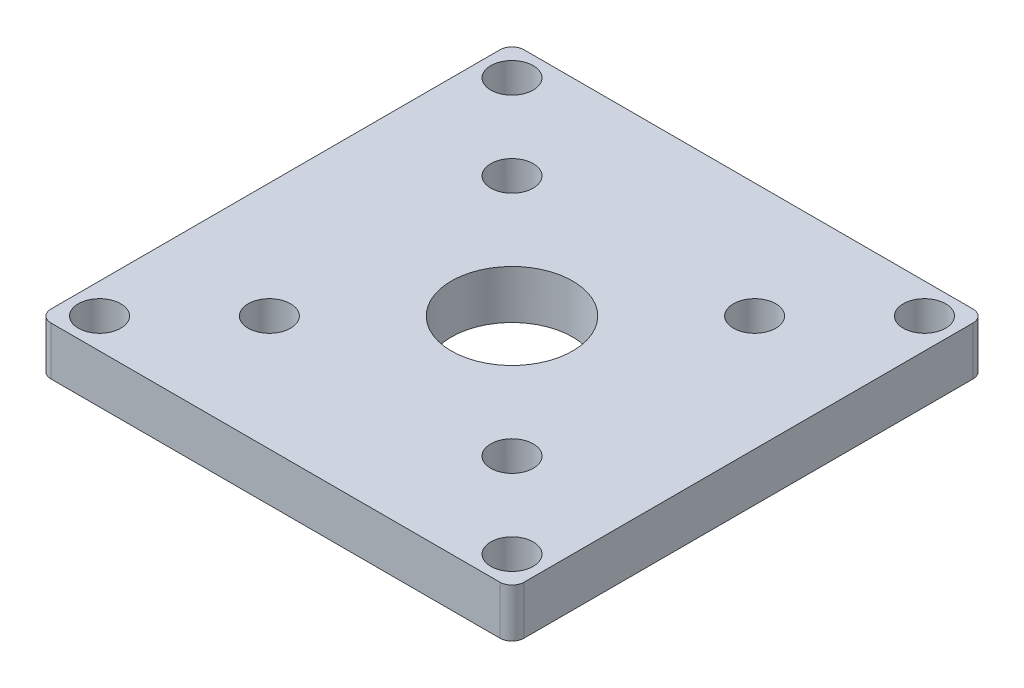
SolidWorks part; units mm, degrees
ref_plane "Front Plane" through (0, 0, 0) normal (0, 0, 1) x (1, 0, 0)
ref_plane "Top Plane" through (0, 0, 0) normal (0, 1, 0) x (1, 0, 0)
ref_plane "Right Plane" through (0, 0, 0) normal (1, 0, 0) x (0, 0, -1)
sketch "Sketch1" plane through (0, 0, 0) normal (0, 1, 0) x (1, 0, 0)
  line L5 (-17, -17) -> (17, -17) construction
  line L6 (-17, -17) -> (-17, 17) construction
  line L7 (-17, 17) -> (17, 17) construction
  line L8 (17, -17) -> (17, 17) construction
  line L9 (-17, -17) -> (17, 17) construction
  line L10 (-17, 17) -> (17, -17) construction
  line L11 (-19.5, -19.5) -> (19.5, -19.5)
  line L12 (-19.5, -19.5) -> (-19.5, 19.5)
  line L13 (-19.5, 19.5) -> (19.5, 19.5)
  line L14 (19.5, -19.5) -> (19.5, 19.5)
  line L15 (-19.5, -19.5) -> (19.5, 19.5) construction
  line L16 (-19.5, 19.5) -> (19.5, -19.5) construction
  circle A0 centre (17, 17) radius 1.75
  circle A1 centre (17, -17) radius 1.75
  circle A2 centre (-17, -17) radius 1.75
  circle A3 centre (-17, 17) radius 1.75
  point P0 (0, 0)
  point P1 (0, 0)
  point P6 (0, 0)
  point P21 (0, 0)
  dimension "D5" = 3.5
  dimension "D1" = 39
  dimension "D2" = 39
  dimension "D3" = 34
  dimension "D4" = 34
  dimension "D6" = 4
extrude "Boss-Extrude1" add sketch "Sketch1" along normal blind 4
sketch "Sketch2" plane through (0, 4, 0) normal (0, 1, 0) x (1, 0, 0)
  line L1 (-10, -10) -> (10, -10) construction
  line L2 (-10, -10) -> (-10, 10) construction
  line L3 (-10, 10) -> (10, 10) construction
  line L4 (10, -10) -> (10, 10) construction
  line L5 (-10, -10) -> (10, 10) construction
  line L6 (-10, 10) -> (10, -10) construction
  circle A0 centre (10, 10) radius 1.75
  circle A1 centre (10, -10) radius 1.75
  circle A2 centre (-10, -10) radius 1.75
  circle A3 centre (-10, 10) radius 1.75
  point P0 (0, 0)
  point P16 (0, 0)
  dimension "D1" = 3.5
  dimension "D2" = 20
  dimension "D3" = 20
  dimension "D4" = 4
extrude "Cut-Extrude1" cut sketch "Sketch2" against normal blind 11
fillet "Fillet1" radius 1 4 edges at (-19.5, 2, 19.5) (-19.5, 2, -19.5) (19.5, 2, -19.5) (19.5, 2, 19.5)
sketch "Sketch3" plane through (0, 4, 0) normal (0, 1, 0) x (1, 0, 0)
  circle A0 centre (0, 0) radius 5
  dimension "D1" = 10
extrude "Cut-Extrude2" cut sketch "Sketch3" against normal up to next
